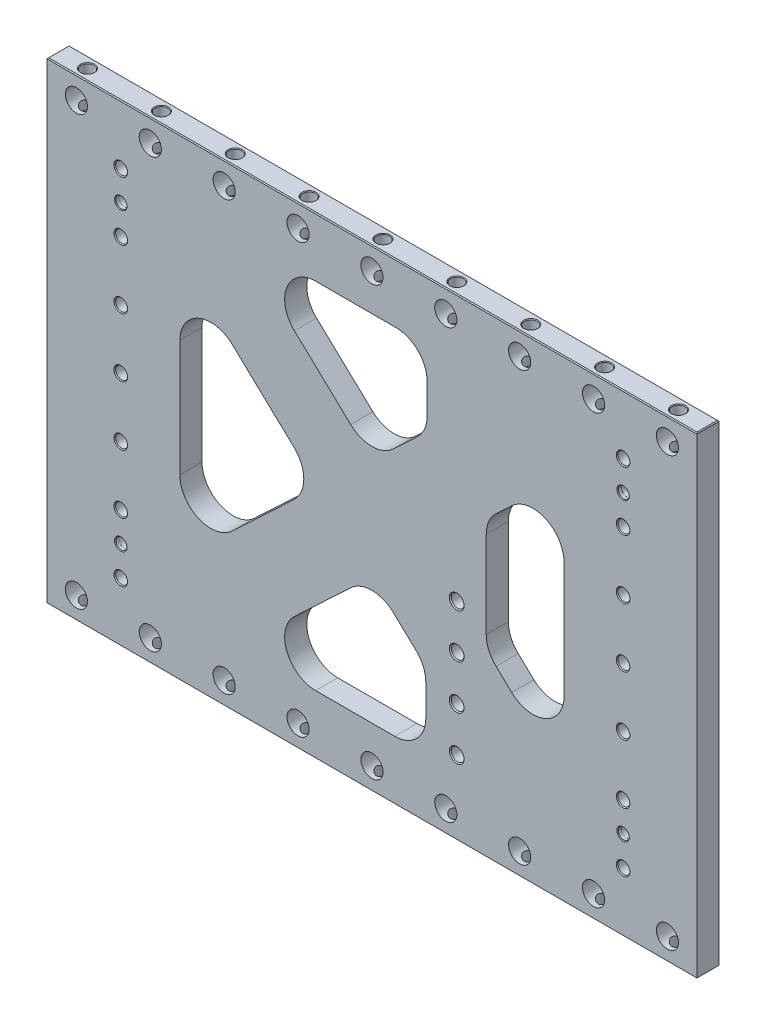
SolidWorks part; units mm, degrees
material "6061-T6 Al"
ref_plane "Front Plane" through (0, 0, 0) normal (0, 0, 1) x (1, 0, 0)
ref_plane "Top Plane" through (0, 0, 0) normal (0, 1, 0) x (1, 0, 0)
ref_plane "Right Plane" through (0, 0, 0) normal (1, 0, 0) x (0, 0, -1)
sketch "Sketch2" plane through (0, 0, 0) normal (0, 0, 1) x (1, 0, 0)
  line L0 (-279.4, -203.2) -> (279.4, 203.2) construction
  line L1 (-279.4, 203.2) -> (279.4, 203.2)
  line L2 (-279.4, 203.2) -> (-279.4, -203.2)
  line L3 (-279.4, -203.2) -> (279.4, -203.2)
  line L4 (279.4, 203.2) -> (279.4, -203.2)
  point P4 (0, 0)
  dimension "D1" = 558.8
  dimension "D2" = 406.4
extrude "Extrude1" add sketch "Sketch2" along normal mid plane 19.05
sketch "Sketch8" plane through (0, 0, 9.525) normal (0, 0, 1) x (1, 0, 0)
  line L0 (-215.9, 203.2) -> (215.9, -203.2) construction
  line L1 (0, 0) -> (-46.3257, 0) construction
  line L2 (-165.1, 111.7876) -> (-46.3257, 0)
  line L3 (-46.3257, 0) -> (-165.1, -111.7876)
  line L4 (-165.1, -111.7876) -> (-165.1, 111.7876)
  line L5 (-115.5993, 152.4) -> (0, 43.6007)
  line L6 (0, 43.6007) -> (47.4665, 88.275)
  line L7 (47.4665, 152.4) -> (-115.5993, 152.4)
  line L8 (165.1, 111.7876) -> (165.1, -111.7876)
  line L9 (165.1, -111.7876) -> (98.2665, -48.8855)
  line L10 (47.4665, 120.3375) -> (98.2665, 120.3375) construction
  line L11 (0, -43.6007) -> (-115.5993, -152.4)
  line L12 (-115.5993, -152.4) -> (46.3257, -152.4)
  line L13 (98.2665, 48.8855) -> (165.1, 111.7876)
  line L14 (215.9, 203.2) -> (-215.9, -203.2) construction
  line L15 (0, 43.6007) -> (0, 0) construction
  line L16 (-279.4, -203.2) -> (279.4, -203.2) construction
  line L17 (0, 0) -> (46.3257, 0) construction
  line L18 (0, 0) -> (0, -43.6007) construction
  line L19 (72.8665, -203.2) -> (72.8665, 203.2) construction
  line L20 (279.4, 203.2) -> (-279.4, 203.2) construction
  line L21 (47.4665, 152.4) -> (47.4665, 88.275)
  line L22 (46.3257, -87.2013) -> (46.3257, -152.4)
  line L23 (98.2665, 48.8855) -> (98.2665, -48.8855)
  line L24 (46.3257, -87.2013) -> (0, -43.6007)
  line L25 (279.4, -203.2) -> (279.4, 203.2) construction
  point P4 (0, 0)
  point P5 (0, 0)
  point P32 (72.8665, 120.3375)
  dimension "D1" = 215.9
  dimension "D2" = 63.5
  dimension "D3" = 50.8
  dimension "D4" = 50.8
  dimension "D5" = 206.5335
  dimension "D6" = 50.8
extrude "Triangles -- Cut-Extrude2" cut sketch "Sketch8" against normal through all
fillet "Triangles -- Fillet1" radius 26.67 15 edges at (-165.1, -111.7876, 0) (-46.3257, 0, 0) (-115.5993, -152.4, 0) (165.1, -111.7876, 0) (-115.5993, 152.4, 0) (0, 43.6007, 0) (-165.1, 111.7876, 0) (98.2665, -48.8855, 0) (165.1, 111.7876, 0) (98.2665, 48.8855, 0) (0, -43.6007, 0) (46.3257, -87.2013, 0) (46.3257, -152.4, 0) (47.4665, 88.275, 0) (47.4665, 152.4, 0)
hole_wizard "CBORE for 3/8 Socket Head Cap Screw2" positions "Sketch4" profile "Sketch3" counterbore size "3/8" standard "Ansi Inch" end condition through all
sketch "Sketch4" plane through (95.7872, 26.66, -9.525) normal (0, 0, 1) x (1, 0, 0)
  line L3 (-95.7872, -26.66) -> (-311.6872, -26.66) construction
  line L7 (-95.7872, -26.66) -> (120.1128, -26.66) construction
  point P0 (-311.6872, -26.66)
  dimension "D1" = 431.8
sketch "Sketch3" plane through (-215.9, 0, -9.525) normal (1, 0, 0) x (0, 1, 0)
  line L0 (0, 0) -> (0, 19.05)
  line L1 (5.1587, 18.264) -> (5.842, 19.05)
  line L2 (5.1587, 18.264) -> (5.1587, 4.318)
  line L3 (5.1587, 4.318) -> (8.7312, 4.318)
  line L4 (8.7312, 4.318) -> (8.7312, 0)
  line L5 (8.7312, 0) -> (0, 0)
  line L11 (0, -6.35) -> (0, 107.95) construction
  line L12 (5.842, 19.05) -> (0, 19.05)
  line L13 (-5.1587, 18.264) -> (-5.842, 19.05) construction
  dimension "Thru Hole Dia." = 10.3175
  dimension "Thru Hole Depth" = 19.05
  dimension "C'Bore Dia." = 17.4625
  dimension "C'Bore Depth" = 4.318
  dimension "Far C'Sink Dia." = 11.684
  dimension "Far C'Sink Angle" = 82
pattern_linear "LPattern3" count 4 spacing 50.8 along (0, 1, 0) count 4 spacing 50.8 along (0, -1, 0) of "CBORE for 3/8 Socket Head Cap Screw2"
mirror "Mirror1" about plane through (0, 0, 0) normal (1, 0, 0) of "LPattern3", "CBORE for 3/8 Socket Head Cap Screw2"
hole_wizard "3/4 (0.75) Diameter Hole1" positions "Sketch11" profile "Sketch10" hole size "3/4" standard "Ansi Inch" end condition through all
sketch "Sketch11" plane through (0, 0, 9.525) normal (0, 0, 1) x (1, 0, 0)
  line L0 (0, 0) -> (0, -184.15) construction
  line L2 (-279.4, -203.2) -> (279.4, -203.2) construction
  point P0 (0, -184.15)
  dimension "D1" = 19.05
sketch "Sketch10" plane through (0, -184.15, 9.525) normal (1, 0, 0) x (0, -1, 0)
  line L0 (0, 0) -> (0, 19.05)
  line L1 (0, 19.05) -> (9.525, 19.05)
  line L2 (9.525, 19.05) -> (9.525, 0)
  line L5 (9.525, 0) -> (0, 0)
  line L11 (0, -6.35) -> (0, 107.95) construction
  dimension "Thru Hole Dia." = 19.05
  dimension "Thru Hole Depth" = 19.05
hole_wizard "7/16 (0.4375) Diameter Hole1" positions "Sketch13" profile "Sketch12" hole size "7/16" standard "Ansi Inch"
sketch "Sketch13" plane through (0, -203.2, 0) normal (0, -1, 0) x (1, 0, 0)
  point P0 (0, 0)
sketch "Sketch12" plane through (0, -203.2, 0) normal (1, 0, 0) x (0, 0, -1)
  line L0 (0, 0) -> (0, 38.2635)
  line L1 (0, 38.2635) -> (5.5562, 34.925)
  line L2 (5.5562, 34.925) -> (5.5562, 0.6209)
  line L3 (5.5562, 0.6209) -> (6.096, 0)
  line L5 (6.096, 0) -> (0, 0)
  line L6 (-5.5562, 0.6209) -> (-6.096, 0) construction
  line L10 (0, 38.2635) -> (-5.5563, 34.925) construction
  line L11 (0, -6.35) -> (0, 107.95) construction
  dimension "Hole Dia." = 11.1125
  dimension "Hole Depth" = 34.925
  dimension "Near C'Sink Dia." = 12.192
  dimension "Near C'Sink Angle" = 82
  dimension "Drill Angle" = 118
pattern_linear "LPattern4" count 5 spacing 63.5 along (1, 0, 0) count 5 spacing 63.5 along (-1, 0, 0) of "7/16 (0.4375) Diameter Hole1", "3/4 (0.75) Diameter Hole1"
mirror "Mirror2" about plane through (0, 0, 0) normal (0, 1, 0) of "LPattern4", "3/4 (0.75) Diameter Hole1", "7/16 (0.4375) Diameter Hole1"
hole_wizard "CBORE for 3/8 Socket Head Cap Screw1" positions "Sketch19" profile "Sketch18" counterbore size "3/8" standard "Ansi Inch" end condition through all
sketch "Sketch19" plane through (0, 0, -9.525) normal (0, 0, -1) x (-1, 0, 0)
  line L16 (279.4, -203.2) -> (-279.4, -203.2) construction
  line L17 (-72.8665, -203.2) -> (-72.8665, 203.2) construction
  point P18 (-72.8665, -139.7)
  dimension "D2" = 63.5
sketch "Sketch18" plane through (72.8665, -139.7, -9.525) normal (1, 0, 0) x (0, 1, 0)
  line L0 (0, 0) -> (0, 19.05)
  line L1 (5.5562, 18.1369) -> (6.35, 19.05)
  line L2 (5.5562, 18.1369) -> (5.5563, 4.318)
  line L3 (5.5563, 4.318) -> (9.1281, 4.318)
  line L4 (9.1281, 4.318) -> (9.1281, 0)
  line L5 (9.1281, 0) -> (0, 0)
  line L11 (0, -6.35) -> (0, 107.95) construction
  line L12 (6.35, 19.05) -> (0, 19.05)
  line L13 (-5.5563, 18.1369) -> (-6.35, 19.05) construction
  dimension "Thru Hole Dia." = 11.1125
  dimension "Thru Hole Depth" = 19.05
  dimension "C'Bore Dia." = 18.2562
  dimension "C'Bore Depth" = 4.318
  dimension "Far C'Sink Dia." = 12.7
  dimension "Far C'Sink Angle" = 82
pattern_linear "LPattern5" count 4 spacing 38.1 along (0, 1, 0) of "CBORE for 3/8 Socket Head Cap Screw1"
hole_wizard "3/8 (0.375) Pin + Lead-In Hole1" positions "Sketch22" profile "Sketch21" counterbore size "3/8" standard "Ansi Inch" end condition through all
sketch "Sketch22" plane through (63.4543, 127.9376, 9.525) normal (0, 0, 1) x (1, 0, 0)
  line L12 (-63.4543, -127.9376) -> (-63.4543, 75.2624) construction
  line L13 (215.9457, 75.2624) -> (-342.8543, 75.2624) construction
  line L14 (215.9457, 75.2624) -> (-342.8543, 75.2624) construction
  line L15 (-63.4543, -127.9376) -> (-425.7771, -127.9376) construction
  point P0 (-279.3543, -0.9376)
  point P54 (152.4457, -0.9376)
  point P77 (152.4457, -254.9376)
  point P78 (-279.3543, -254.9376)
  dimension "D1" = 76.2
sketch "Sketch21" plane through (-215.9, 127, 9.525) normal (1, 0, 0) x (0, -1, 0)
  line L0 (0, 0) -> (0, 19.05)
  line L1 (0, 19.05) -> (4.7625, 19.05)
  line L3 (4.7625, 19.05) -> (4.7625, 3.175)
  line L4 (4.7879, 3.175) -> (4.7625, 3.175)
  line L5 (4.7879, 3.175) -> (4.7879, 0.6282)
  line L6 (4.7879, 0.6282) -> (5.334, 0)
  line L7 (5.334, 0) -> (0, 0)
  line L8 (-4.7879, 0.6282) -> (-5.334, 0) construction
  line L11 (0, -6.35) -> (0, 107.95) construction
  dimension "Thru Hole Dia." = 9.525
  dimension "Thru Hole Depth" = 19.05
  dimension "C'Bore Dia." = 9.5758
  dimension "C'Bore Depth" = 3.175
  dimension "Near C'Sink Dia." = 10.668
  dimension "Near C'Sink Angle" = 82
chamfer "Chamfer1" distance 0.762 angle 45 8 edges at (279.4, -203.2, 0) (0, -203.2, 9.525) (0, -203.2, -9.525) (-279.4, -203.2, 0) (-279.4, 203.2, 0) (0, 203.2, -9.525) (279.4, 203.2, 0) (0, 203.2, 9.525)
